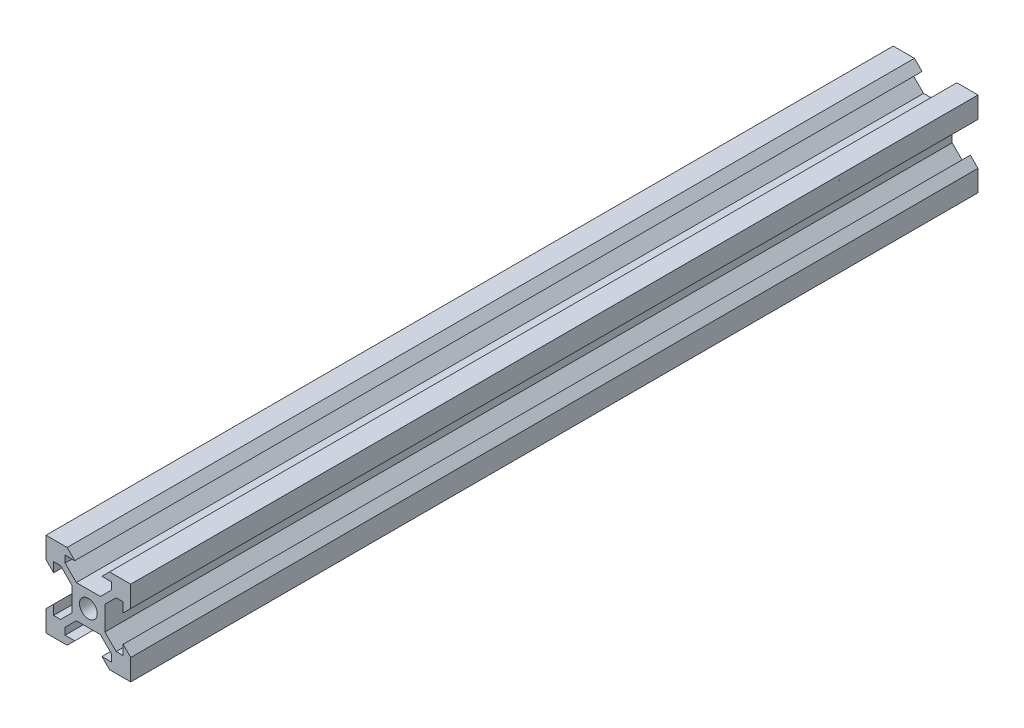
SolidWorks part; units mm, degrees
material "6063-T5"
ref_plane "Front Plane" through (0, 0, 0) normal (0, 0, 1) x (1, 0, 0)
ref_plane "Top Plane" through (0, 0, 0) normal (0, 1, 0) x (1, 0, 0)
ref_plane "Right Plane" through (0, 0, 0) normal (1, 0, 0) x (0, 0, -1)
sketch "Sketch1" plane through (0, 0, 0) normal (0, 0, 1) x (1, 0, 0)
  line L0 (-10, 10) -> (-5, 10)
  line L1 (10, -10) -> (-10, -10) construction
  line L2 (10, -10) -> (10, 10) construction
  line L3 (10, 10) -> (-10, 10) construction
  line L4 (-10, -10) -> (-10, 10) construction
  line L5 (10, -10) -> (-10, 10) construction
  line L6 (10, 10) -> (-10, -10) construction
  line L7 (-5, 10) -> (-3.2, 8.2)
  line L8 (-3.2, 8.2) -> (-5.4993, 8.2)
  line L9 (-5.4993, 8.2) -> (-5.4993, 6.56)
  line L10 (-2.84, 3.9007) -> (2.84, 3.9007)
  line L11 (0, 3.9007) -> (0, 2.1) construction
  line L12 (-5.4993, 6.56) -> (-2.84, 3.9007)
  line L13 (0, 0) -> (0, -13.2939) construction
  line L14 (0, 0) -> (-17.0802, 0) construction
  line L15 (-10, 10) -> (-10, 5)
  line L16 (-10, 5) -> (-8.2, 3.2)
  line L17 (-8.2, 3.2) -> (-8.2, 5.4993)
  line L18 (-8.2, 5.4993) -> (-6.56, 5.4993)
  line L19 (-6.56, 5.4993) -> (-3.9007, 2.84)
  line L20 (-3.9007, 2.84) -> (-3.9007, -2.84)
  line L21 (-3.2, -8.2) -> (-5.4993, -8.2)
  line L22 (-5.4993, -8.2) -> (-5.4993, -6.56)
  line L23 (-5, -10) -> (-3.2, -8.2)
  line L24 (-10, -10) -> (-5, -10)
  line L25 (-10, -10) -> (-10, -5)
  line L26 (-10, -5) -> (-8.2, -3.2)
  line L27 (-8.2, -3.2) -> (-8.2, -5.4993)
  line L28 (-8.2, -5.4993) -> (-6.56, -5.4993)
  line L29 (-6.56, -5.4993) -> (-3.9007, -2.84)
  line L30 (-5.4993, -6.56) -> (-2.84, -3.9007)
  line L31 (-2.84, -3.9007) -> (2.84, -3.9007)
  line L32 (5.4993, 6.56) -> (2.84, 3.9007)
  line L33 (3.2, 8.2) -> (5.4993, 8.2)
  line L34 (5.4993, 8.2) -> (5.4993, 6.56)
  line L35 (5, 10) -> (3.2, 8.2)
  line L36 (10, 10) -> (5, 10)
  line L37 (10, 10) -> (10, 5)
  line L38 (10, 5) -> (8.2, 3.2)
  line L39 (8.2, 3.2) -> (8.2, 5.4993)
  line L40 (8.2, 5.4993) -> (6.56, 5.4993)
  line L41 (6.56, 5.4993) -> (3.9007, 2.84)
  line L42 (3.9007, 2.84) -> (3.9007, -2.84)
  line L43 (6.56, -5.4993) -> (3.9007, -2.84)
  line L44 (8.2, -5.4993) -> (6.56, -5.4993)
  line L45 (8.2, -3.2) -> (8.2, -5.4993)
  line L46 (10, -5) -> (8.2, -3.2)
  line L47 (10, -10) -> (10, -5)
  line L48 (10, -10) -> (5, -10)
  line L49 (5, -10) -> (3.2, -8.2)
  line L50 (3.2, -8.2) -> (5.4993, -8.2)
  line L51 (5.4993, -8.2) -> (5.4993, -6.56)
  line L52 (5.4993, -6.56) -> (2.84, -3.9007)
  circle A0 centre (0, 0) radius 2.1
  arc A1 (0, -2.1) -> (0, 2.1) centre (0, 0) cw construction
  point P0 (0, 0)
  point P25 (-3.9007, 0)
  point P35 (0, 0)
  point P56 (0, -3.9007)
  dimension "D2" = 4.2
  dimension "D1" = 20
  dimension "D3" = 1.64
  dimension "D4" = 1.8
  dimension "D5" = 45
  dimension "D6" = 1.5
  dimension "D7" = 5.68
  dimension "D8" = 5
extrude "Boss-Extrude1" add sketch "Sketch1" along normal mid plane 200.025
